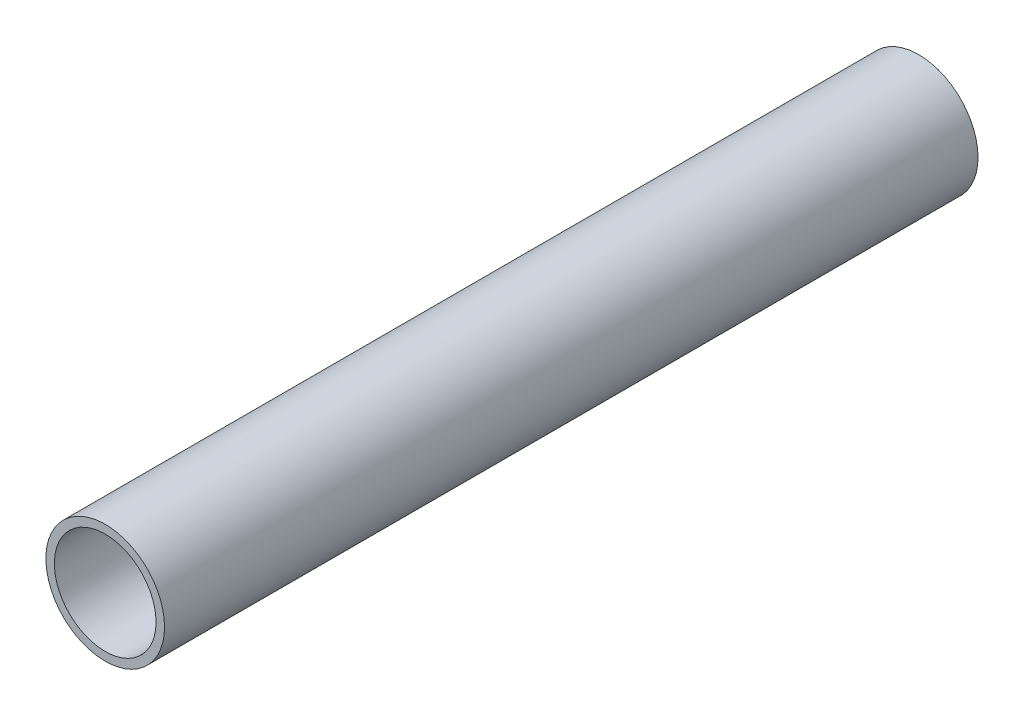
SolidWorks part; units mm, degrees
ref_plane "Front" through (0, 0, 0) normal (0, 0, 1) x (1, 0, 0)
ref_plane "Top" through (0, 0, 0) normal (0, 1, 0) x (1, 0, 0)
ref_plane "Right" through (0, 0, 0) normal (1, 0, 0) x (0, 0, -1)
sketch "Sketch1" plane through (0, 0, 0) normal (0, 0, 1) x (1, 0, 0)
  circle A0 centre (0, 0) radius 9.525
  dimension "D1" = 19.05
extrude "Extrude-Thin1" add sketch "Sketch1" against normal blind 152.4 thin
